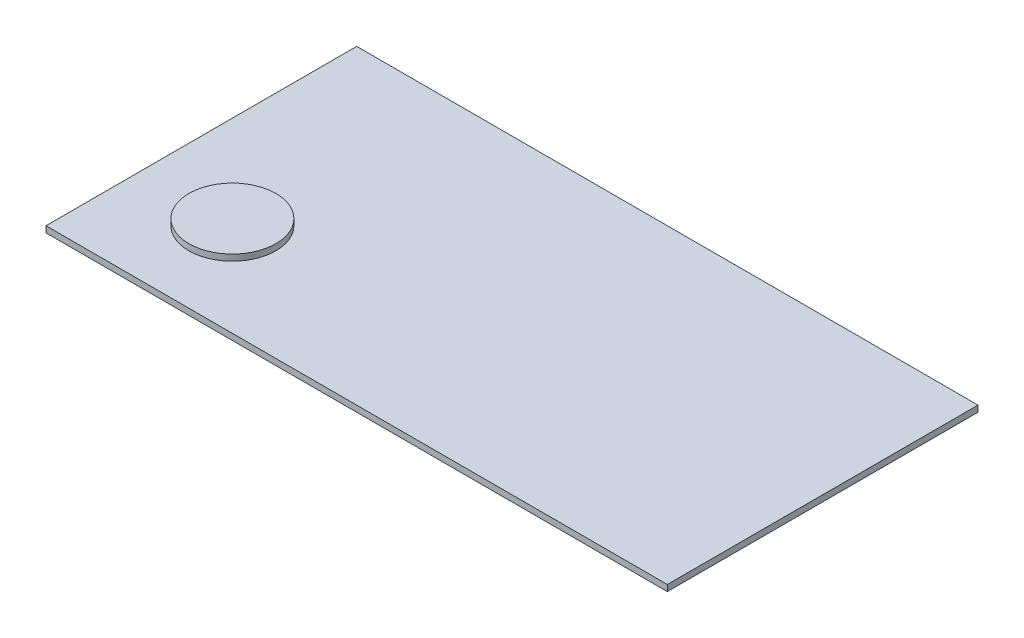
SolidWorks part; units mm, degrees
ref_plane "Front Plane" through (0, 0, 0) normal (0, 0, 1) x (1, 0, 0)
ref_plane "Top Plane" through (0, 0, 0) normal (0, 1, 0) x (1, 0, 0)
ref_plane "Right Plane" through (0, 0, 0) normal (1, 0, 0) x (0, 0, -1)
sketch "Sketch1" plane through (0, 0, 0) normal (0, 1, 0) x (1, 0, 0)
  line L1 (-500, 250) -> (500, 250)
  line L2 (-500, 250) -> (-500, -250)
  line L3 (-500, -250) -> (500, -250)
  line L4 (500, 250) -> (500, -250)
  line L5 (-500, 250) -> (500, -250) construction
  line L6 (-500, -250) -> (500, 250) construction
  point P0 (0, 0)
  dimension "D1" = 1000
  dimension "D2" = 500
extrude "Boss-Extrude1" add sketch "Sketch1" along normal blind 10
ref_plane "Plane1" through (0, 10, 0) normal (0, 1, 0) x (1, 0, 0)
sketch "Sketch2" plane through (0, 10, 0) normal (0, 1, 0) x (1, 0, 0)
  line L0 (-500, 250) -> (-500, -250) construction
  line L1 (-500, -250) -> (500, -250) construction
  circle A0 centre (-350, -100) radius 70
  dimension "D1" = 140
  dimension "D2" = 150
  dimension "D3" = 150
extrude "Boss-Extrude2" add sketch "Sketch2" along normal blind 10
